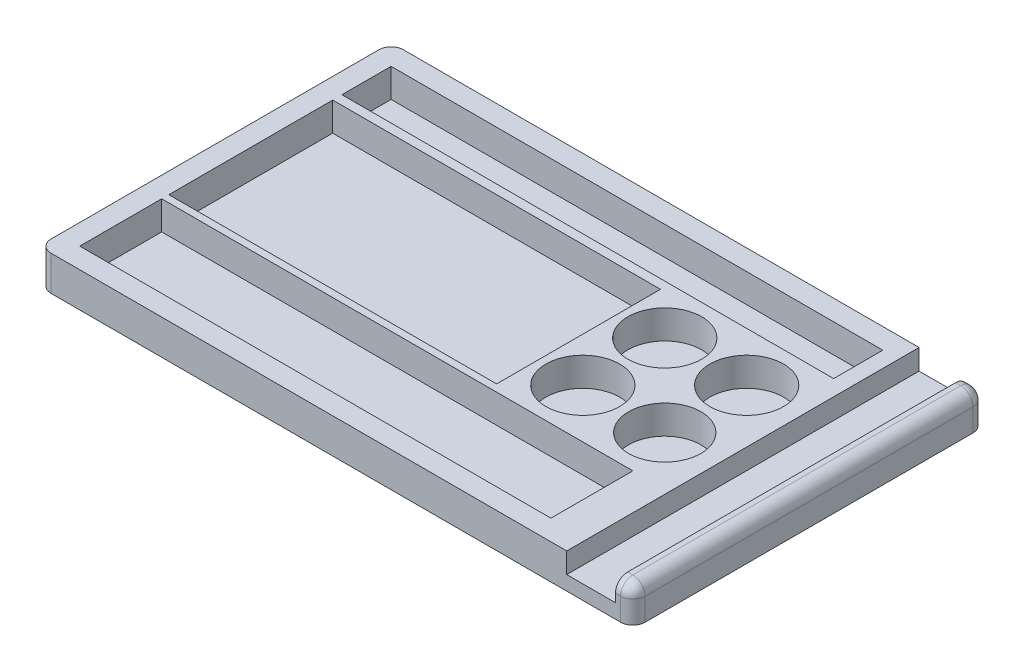
SolidWorks part; units mm, degrees
ref_plane "Спереди" through (0, 0, 0) normal (0, 0, 1) x (1, 0, 0)
ref_plane "Сверху" through (0, 0, 0) normal (0, 1, 0) x (1, 0, 0)
ref_plane "Справа" through (0, 0, 0) normal (1, 0, 0) x (0, 0, -1)
other "Configuration Table"
sketch "Эскиз1" plane through (0, 0, 0) normal (0, 1, 0) x (1, 0, 0)
  line L1 (0, 0) -> (145, 0)
  line L2 (0, 0) -> (0, 86)
  line L3 (0, 86) -> (145, 86)
  line L4 (145, 0) -> (145, 86)
  dimension "D1" = 86
  dimension "D2" = 145
extrude "основа" add sketch "Эскиз1" along normal blind 8.5
sketch "Эскиз4" plane through (0, 8.5, 0) normal (0, 1, 0) x (1, 0, 0)
  line L0 (-9.4894, 46.7409) -> (153.2017, 46.7409) construction
  line L1 (0, 86) -> (0, 0) construction
  line L2 (85, 26.7409) -> (5, 26.7409)
  line L3 (85, 26.7409) -> (85, 66.7409)
  line L4 (85, 66.7409) -> (5, 66.7409)
  line L5 (5, 26.7409) -> (5, 66.7409)
  line L6 (85, 26.7409) -> (5, 66.7409) construction
  line L7 (85, 66.7409) -> (5, 26.7409) construction
  point P2 (45, 46.7409)
  point P7 (-4.8102, 53.4639)
  dimension "D1" = 80
  dimension "D2" = 40
  dimension "D3" = 5
extrude "Вырез-Вытянуть1" cut sketch "Эскиз4" against normal blind 7
sketch "Эскиз6" plane through (0, 8.5, 0) normal (0, 1, 0) x (1, 0, 0)
  line L0 (2.4746, 15) -> (154.2259, 15) construction
  line L1 (0, 86) -> (0, 0) construction
  line L2 (120, 5) -> (5, 5)
  line L3 (120, 5) -> (120, 25)
  line L4 (120, 25) -> (5, 25)
  line L5 (5, 5) -> (5, 25)
  line L6 (120, 5) -> (5, 25) construction
  line L7 (120, 25) -> (5, 5) construction
  line L9 (0, 0) -> (145, 0) construction
  point P2 (62.5, 15)
  dimension "D1" = 20
  dimension "D2" = 115
  dimension "D3" = 5
  dimension "D4" = 5
extrude "Вырез отвертка" cut sketch "Эскиз6" against normal blind 7
sketch "Эскиз8" plane through (0, 8.5, 0) normal (0, 1, 0) x (1, 0, 0)
  line L0 (-48.7487, 75) -> (103.0026, 75) construction
  line L1 (145, 86) -> (0, 86) construction
  line L2 (125, 69) -> (5, 69)
  line L3 (125, 69) -> (125, 81)
  line L4 (125, 81) -> (5, 81)
  line L5 (5, 69) -> (5, 81)
  line L6 (125, 69) -> (5, 81) construction
  line L7 (125, 81) -> (5, 69) construction
  line L8 (0, 86) -> (0, 0) construction
  point P2 (65, 75)
  dimension "D1" = 12
  dimension "D2" = 120
  dimension "D3" = 5
  dimension "D4" = 5
extrude "Вырез-Вытянуть5" cut sketch "Эскиз8" against normal blind 7
sketch "Эскиз14" plane through (0, 8.5, 0) normal (0, 1, 0) x (1, 0, 0)
  line L0 (84.6933, 36.9757) -> (124.6385, 36.9757) construction
  line L1 (95.8072, 26.9653) -> (95.8072, 66.6577) construction
  line L2 (115.8072, 26.9653) -> (115.8072, 66.6577) construction
  line L3 (85.3226, 56.9757) -> (125.7799, 56.9757) construction
  line L4 (90.4415, 46.8115) -> (123.2738, 46.8115) construction
  line L5 (88.7817, 46.8351) -> (4.1216, 46.8351) construction
  circle A0 centre (95.8072, 36.9757) radius 9
  circle A1 centre (115.8072, 36.9757) radius 8.8313
  circle A2 centre (95.8072, 56.9757) radius 9
  circle A3 centre (115.8072, 56.9757) radius 9
  dimension "D1" = 18
  dimension "D2" = 20
  dimension "D3" = 20
extrude "Вырез-Вытянуть11" cut sketch "Эскиз14" against normal blind 7
sketch "Эскиз15" plane through (0, 8.5, 0) normal (0, 1, 0) x (1, 0, 0)
  line L0 (145, 86) -> (0, 86) construction
  line L1 (128.8564, 86) -> (140.7441, 86)
  line L2 (128.8564, 86) -> (128.8564, 0)
  line L3 (128.8564, 0) -> (140.7441, 0)
  line L4 (140.7441, 86) -> (140.7441, 0)
  line L5 (0, 0) -> (145, 0) construction
extrude "Вырез-Вытянуть12" cut sketch "Эскиз15" against normal blind 5
fillet "Скругление1" radius 3 1 edges at (145, 8.5, -43)
fillet "Скругление2" radius 3 3 edges at (141.372, 8.5, 0) (144.1213, 7.6213, 0) (145, 2.75, 0)
fillet "Скругление3" radius 3 3 edges at (141.372, 8.5, -86) (144.1213, 7.6213, -86) (145, 2.75, -86)
fillet "Скругление4" radius 3 1 edges at (0, 4.25, 0)
fillet "Скругление5" radius 3 1 edges at (0, 4.25, -86)
